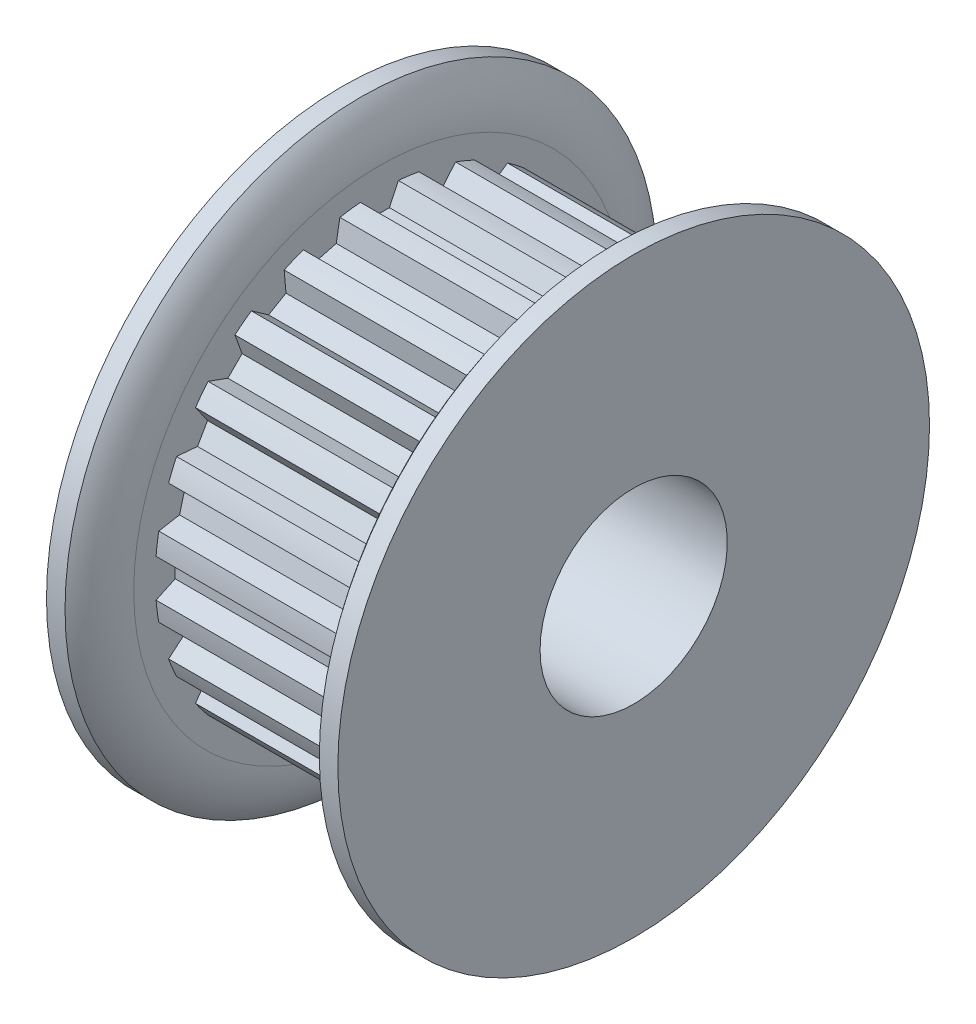
SolidWorks part; units mm, degrees
ref_plane "Front Plane" through (0, 0, 0) normal (0, 0, 1) x (1, 0, 0)
ref_plane "Top Plane" through (0, 0, 0) normal (0, 1, 0) x (1, 0, 0)
ref_plane "Right Plane" through (0, 0, 0) normal (1, 0, 0) x (0, 0, -1)
sketch "Sketch2" plane through (0, 0, 0) normal (1, 0, 0) x (0, 0, -1)
  line L3 (0, 0) -> (0, 6.9342) construction
  line L6 (0, -7.4422) -> (0, -7.7597) construction
  line L7 (-0.5715, 7.4202) -> (-0.341, 6.9258)
  line L8 (0.5715, 7.4202) -> (0.341, 6.9258)
  line L9 (-0.5715, 7.4202) -> (-0.6431, 7.5737)
  line L10 (0.5715, 7.4202) -> (0.6431, 7.5737)
  line L12 (-0.341, 6.9258) -> (0.341, 6.9258)
  line L14 (0, 7.4422) -> (0, 7.7597) construction
  line L15 (0, 0) -> (0, -1.143) construction
  circle A0 centre (0, 0) radius 7.7597 construction
  circle A1 centre (0, 0) radius 6.9342 construction
  circle A2 centre (0, 0) radius 7.4422 construction
  arc A7 (0.6431, 7.5737) -> (-0.6431, 7.5737) centre (0, 0) ccw
  point P5 (0, 7.6009)
  dimension "D3" = 0.3175
  dimension "D1" = 50
sketch "Sketch1" plane through (0, 0, 0) normal (0, 0, 1) x (1, 0, 0)
  line L0 (-8.7376, 0) -> (8.7376, 0) construction
  line L1 (-8.7376, 3.175) -> (8.7376, 3.175)
  line L2 (-8.7376, 3.175) -> (-8.7376, 5.6134)
  line L3 (-1.143, 10.033) -> (-0.5144, 10.033)
  line L4 (0.1143, 7.7597) -> (0.1143, 8.3312)
  line L5 (0.1143, 8.9027) -> (0.1143, 7.7597) construction
  line L6 (0.1143, 7.7597) -> (7.4803, 7.7597)
  line L7 (7.4803, 7.7597) -> (7.4803, 8.3312)
  line L8 (7.4803, 7.7597) -> (8.7376, 7.7597) construction
  line L9 (8.1089, 10.033) -> (8.7376, 10.033)
  line L10 (8.7376, 10.033) -> (8.7376, 3.175)
  line L11 (8.1089, 7.7597) -> (8.1089, 10.033) construction
  line L12 (-4.9403, 5.6134) -> (-4.9403, 3.175) construction
  line L13 (-1.143, 10.033) -> (-1.143, 5.6134)
  line L14 (-1.143, 5.6134) -> (-8.7376, 5.6134)
  arc A0 (7.4803, 8.3312) -> (8.1089, 10.033) centre (10.0981, 8.3312) cw
  arc A1 (0.1143, 8.3312) -> (-0.5144, 10.033) centre (-2.5035, 8.3312) ccw
  dimension "Bore Size" = 6.35
  dimension "Overall Width" = 17.4752
  dimension "Inside Width" = 7.366
  dimension "OD" = 20.066
  dimension "D2" = 15.5194
  dimension "D3" = 1.143
  dimension "D4" = 0.5715
  dimension "Outside Width" = 9.8806
revolve "Revolve1" add sketch "Sketch1" angle 360 mid plane about L0
sketch "Sketch4" plane through (0.1143, 0, 0) normal (1, 0, 0) x (0, 0, -1)
  circle A0 centre (0, 0) radius 7.601
  circle A2 centre (0, 0) radius 7.7597
  circle A3 centre (0, 0) radius 7.7597 construction
extrude "Cut-Extrude2" cut sketch "Sketch4" along normal up to surface (7.366 mm away) up to face at (7.4803, 0, 7.7597)
sketch "Sketch3" plane through (0.1143, 0, 0) normal (1, 0, 0) x (0, 0, -1)
  line L2 (-0.5715, 7.4202) -> (-0.341, 6.9258) construction
  line L3 (-0.341, 6.9258) -> (0.341, 6.9258) construction
  line L4 (0.5715, 7.4202) -> (0.341, 6.9258) construction
  line L5 (-0.6431, 7.5737) -> (-0.341, 6.9258)
  line L6 (-0.341, 6.9258) -> (0.341, 6.9258)
  line L7 (0.6431, 7.5737) -> (0.341, 6.9258)
  arc A1 (0.6431, 7.5737) -> (-0.6431, 7.5737) centre (0, 0) ccw construction
  arc A2 (0.6431, 7.5737) -> (-0.6431, 7.5737) centre (0, 0) ccw
extrude "Cut-Extrude1" cut sketch "Sketch3" along normal up to surface (7.366 mm away) up to face at (7.4803, 0, 8.3312)
pattern_circular "CirPattern1" count 24 over 360 about axis through (0, 0, 0) along (1, 0, 0) of "Cut-Extrude1"
sketch "Sketch5" plane through (0, 0, 0) normal (0, 0, 1) x (1, 0, 0)
  line L1 (7.4803, 8.3312) -> (7.4803, -8.3312) construction
  point P0 (7.4803, 0)
sketch "Sketch6" plane through (0, 0, 0) normal (0, 1, 0) x (1, 0, 0)
  line L0 (-8.7376, 0) -> (-6.4008, 0) construction
  line L1 (-8.7376, 10.033) -> (-8.7376, -10.033) construction
  line L2 (-1.143, 0) -> (-3.4798, 0) construction
  line L4 (-1.143, 10.033) -> (-1.143, -10.033) construction
  circle A0 centre (-4.9403, 0) radius 1.4605
  dimension "D1" = 2.921
extrude "Cut-Extrude3" cut sketch "Sketch6" along normal through all
sketch "Sketch7" plane through (0, 0, 0) normal (0, 0, 1) x (1, 0, 0)
  line L0 (-6.1087, 5.6134) -> (-4.9403, 5.6134)
  line L1 (-6.3627, 5.3594) -> (-6.3627, 3.81)
  line L2 (-6.3627, 3.81) -> (-6.1087, 3.556)
  line L3 (-6.1087, 3.556) -> (-4.9403, 3.556)
  line L4 (-4.9403, 3.556) -> (-4.9403, 5.6134) construction
  line L5 (-1.143, 5.6134) -> (-8.7376, 5.6134) construction
  line L6 (-6.3627, 5.3594) -> (-6.1087, 5.6134)
  line L8 (-4.9403, 5.6134) -> (-4.9403, 3.556)
  point P0 (-6.3627, 5.6134)
  point P4 (-6.3627, 3.556)
  dimension "D1" = 2.8448
  dimension "D2" = 0.381
revolve "Revolve2" add sketch "Sketch7" angle 360 mid plane about L4
sketch "Sketch8" plane through (0, 5.6134, 0) normal (0, 1, 0) x (1, 0, 0)
  line L1 (-4.9403, 0.8212) -> (-5.6515, 0.4106)
  line L2 (-5.6515, 0.4106) -> (-5.6515, -0.4106)
  line L3 (-5.6515, -0.4106) -> (-4.9403, -0.8212)
  line L4 (-4.9403, -0.8212) -> (-4.2291, -0.4106)
  line L5 (-4.2291, -0.4106) -> (-4.2291, 0.4106)
  line L6 (-4.2291, 0.4106) -> (-4.9403, 0.8212)
  circle A0 centre (-4.9403, 0) radius 0.7112 construction
  dimension "D1" = 1.4224
extrude "Cut-Extrude4" cut sketch "Sketch8" against normal blind 1.016
pattern_circular "CirPattern2" count 2 over 90 about axis through (-8.7376, 0, 0) along (-1, 0, 0) of "Cut-Extrude3"
pattern_circular "CirPattern3" count 2 over 90 about axis through (0, 0, 0) along (1, 0, 0) of bodies 107
sketch "Sketch9" plane through (0, 0, 0) normal (0, 1, 0) x (1, 0, 0)
  line L0 (-1.143, 10.033) -> (-1.143, -10.033) construction
  line L1 (-9.191, 8.0798) -> (-1.143, 8.0798)
  line L2 (-9.191, 8.0798) -> (-9.191, -7.7485)
  line L3 (-9.191, -7.7485) -> (-1.143, -7.7485)
  line L4 (-1.143, 8.0798) -> (-1.143, -7.7485)
extrude "Cut-Extrude5" cut sketch "Sketch9" against normal mid plane 15.24
equation "\"D3@Sketch2\" = (\"hs@Sketch2\"-\"ht@Sketch2\")/2"
equation "\"D2@Sketch1\" = \"PD@Sketch2\""
equation "\"D3@Sketch1\" = \"hs@Sketch2\""
equation "\"D4@Sketch1\" = \"D3@Sketch1\"/2"
